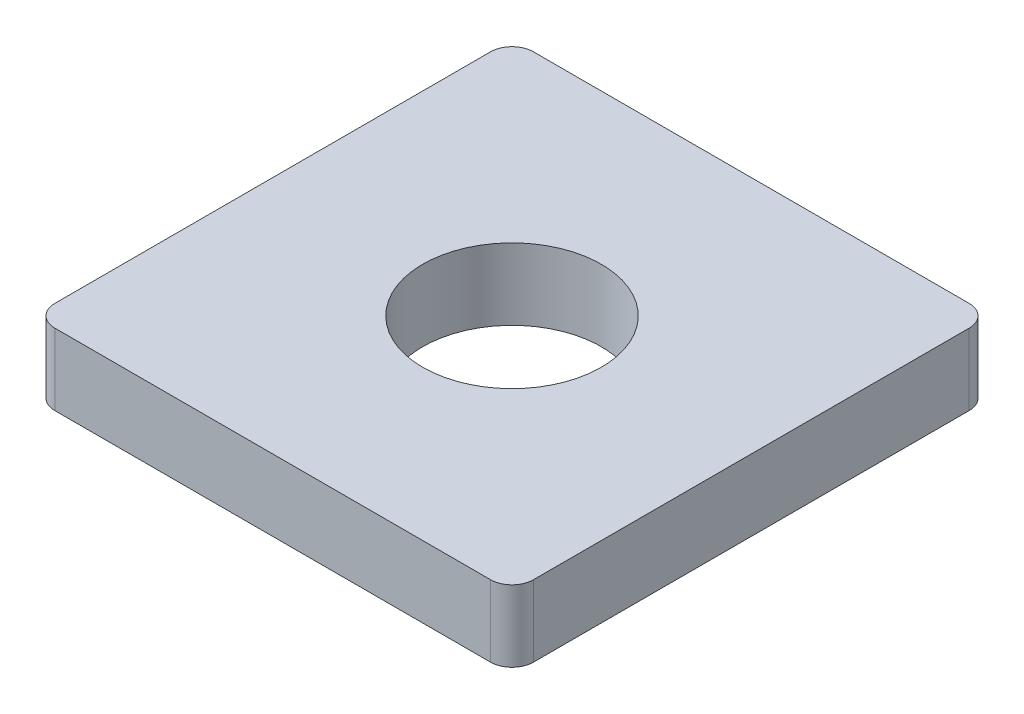
SolidWorks part; units mm, degrees
material "6061 Alloy"
ref_plane "Front Plane" through (0, 0, 0) normal (0, 0, 1) x (1, 0, 0)
ref_plane "Top Plane" through (0, 0, 0) normal (0, 1, 0) x (1, 0, 0)
ref_plane "Right Plane" through (0, 0, 0) normal (1, 0, 0) x (0, 0, -1)
sketch "Sketch1" plane through (0, 0, 0) normal (0, 1, 0) x (1, 0, 0)
  line L1 (-3.35, 3.35) -> (3.35, 3.35)
  line L2 (-3.35, 3.35) -> (-3.35, -3.35)
  line L3 (-3.35, -3.35) -> (3.35, -3.35)
  line L4 (3.35, 3.35) -> (3.35, -3.35)
  line L5 (-3.35, 3.35) -> (3.35, -3.35) construction
  line L6 (-3.35, -3.35) -> (3.35, 3.35) construction
  point P0 (0, 0)
  dimension "D1" = 6.7
extrude "Boss-Extrude1" add sketch "Sketch1" along normal blind 1
hole_wizard "M3x0.5 Tapped Hole1" positions "Sketch2" profile "Sketch3" tap size "M3x0.5" standard "ANSI Metric" end condition through all
sketch "Sketch2" plane through (0, 1, 0) normal (0, 1, 0) x (1, 0, 0)
  point P0 (0, 0)
cosmetic thread "Hole Thread1" parameters "D2"=3
sketch "Sketch3" plane through (0, 1, 0) normal (1, 0, 0) x (0, 0, 1)
  line L0 (0, 0) -> (0, 1)
  line L1 (0, 1) -> (1.25, 1)
  line L2 (1.25, 1) -> (1.25, 0)
  line L5 (1.25, 0) -> (0, 0)
  line L11 (0, -6.35) -> (0, 107.95) construction
  dimension "Thru Tap Drill Dia." = 2.5
  dimension "Thru Tap Drill Depth" = 1
fillet "Fillet1" radius 0.3 4 edges at (-3.35, 0.5, -3.35) (3.35, 0.5, -3.35) (3.35, 0.5, 3.35) (-3.35, 0.5, 3.35)
